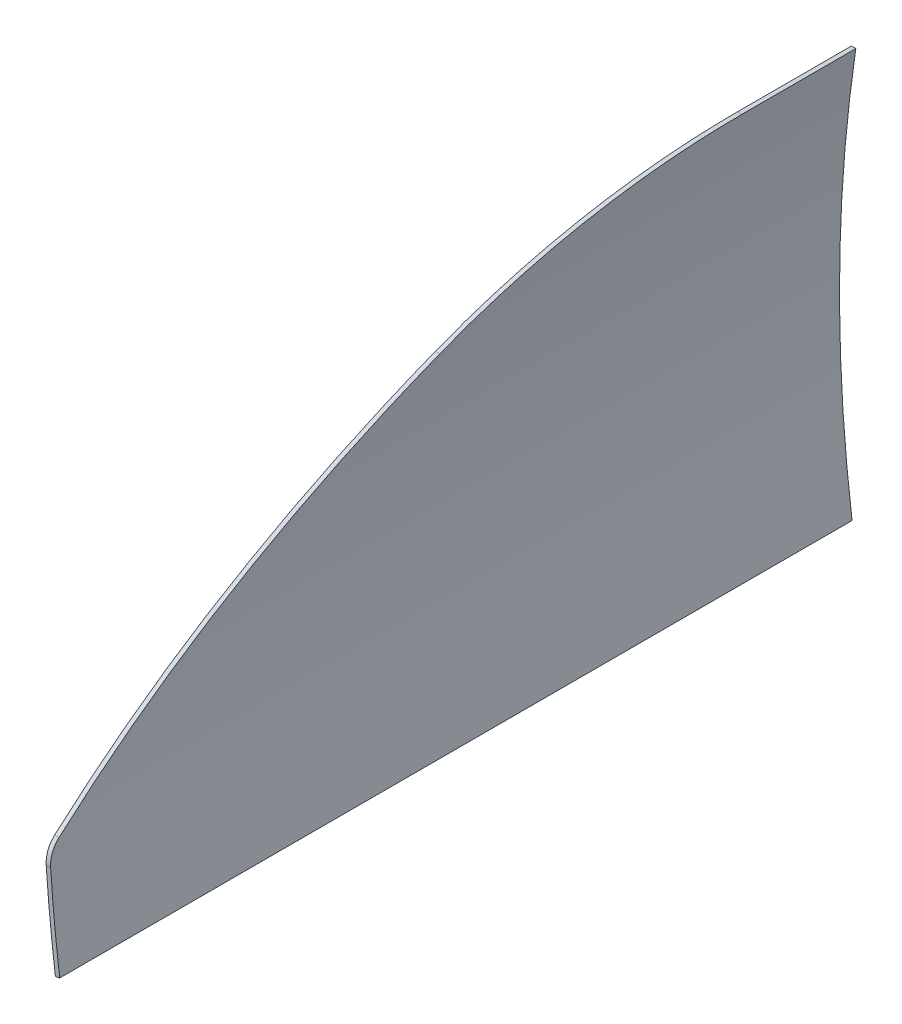
SolidWorks part; units mm, degrees
ref_plane "Front Plane" through (0, 0, 0) normal (0, 0, 1) x (1, 0, 0)
ref_plane "Top Plane" through (0, 0, 0) normal (0, 1, 0) x (1, 0, 0)
ref_plane "Right Plane" through (0, 0, 0) normal (1, 0, 0) x (0, 0, -1)
sketch "Sketch1" plane through (0, 0, 0) normal (0, 0, 1) x (1, 0, 0)
  arc A0 (0, 0) -> (0, 500) centre (1662.9127, 250) cw
  dimension "D2" = 1681.6
  dimension "D1" = 500
extrude "Extrude-Thin1" add sketch "Sketch1" along normal mid plane 1000 thin thin type mid plane wall 5
sketch "Sketch2" plane through (0, 0, 0) normal (1, 0, 0) x (0, 0, -1)
  line L6 (500, 499.6283) -> (370, 499.6283)
  line L7 (-500, 499.6283) -> (500, 499.6283) construction
  line L13 (-404, 30.1883) -> (500, 30.1883)
  line L14 (500, 30.1883) -> (500, 499.6283)
  line L15 (-404, 30.1883) -> (-404, 135.1883)
  arc A1 (370, 499.6283) -> (34.5992, 425.9246) centre (370, -300.3717) ccw
  arc A2 (34.5992, 425.9246) -> (-392.9914, 158.4117) centre (873.1013, -1389.8161) ccw
  arc A4 (-404, 135.1883) -> (-392.9914, 158.4117) centre (-374, 135.1883) cw
  point P5 (0, 0)
  point P17 (-398.8682, 125.4804)
  point P20 (-500, 279.0366)
  dimension "D1" = 130
  dimension "D2" = 904
  dimension "D7" = 800
  dimension "D8" = 2000
  dimension "D6" = 30
  dimension "D3" = 105
extrude "Cut-Extrude1" cut sketch "Sketch2" against normal mid plane 80 flip side to cut
sketch "Sketch3" plane through (0, 0, 404) normal (0, 0, 1) x (1, 0, 0)
  line L0 (-6.7806, 30.1883) -> (-1.8582, 31.1057)
  line L1 (-1.8582, 31.1057) -> (-1.7373, 30.1883)
  line L2 (-1.7373, 30.1883) -> (-6.7806, 30.1883)
  arc A0 (-12.2575, 135.1883) -> (-1.7373, 30.1883) centre (1662.9127, 250) ccw construction
extrude "Cut-Extrude2" cut sketch "Sketch3" against normal through all
